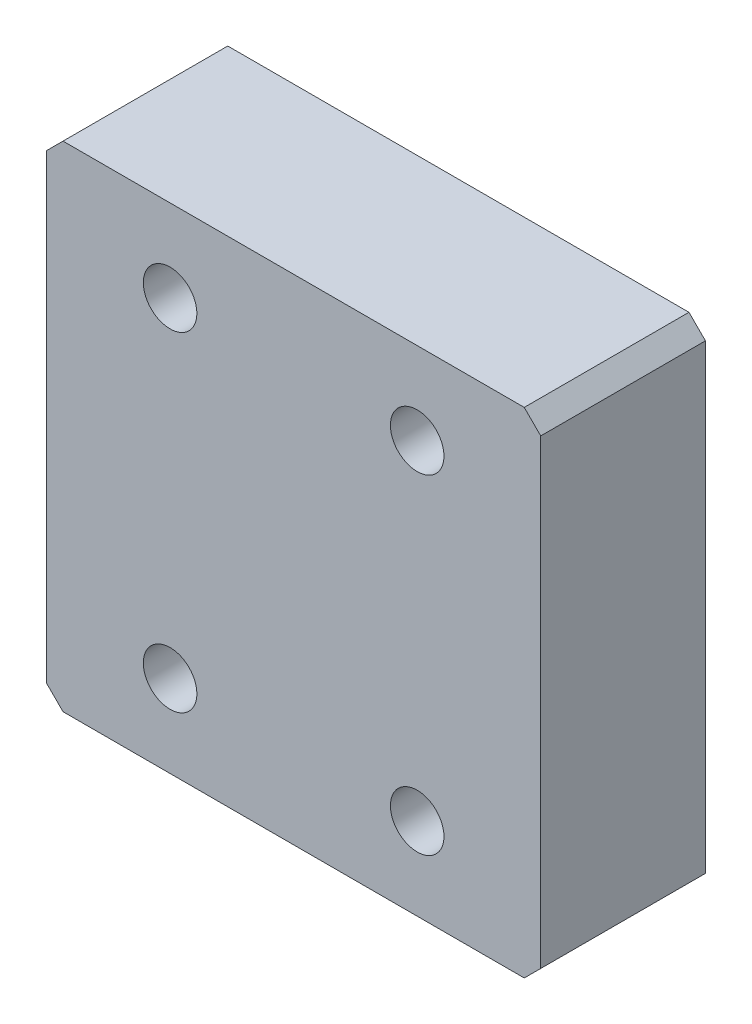
SolidWorks part; units mm, degrees
ref_plane "Front Plane" through (0, 0, 0) normal (0, 0, 1) x (1, 0, 0)
ref_plane "Top Plane" through (0, 0, 0) normal (0, 1, 0) x (1, 0, 0)
ref_plane "Right Plane" through (0, 0, 0) normal (1, 0, 0) x (0, 0, -1)
sketch "Sketch1" plane through (0, 0, 0) normal (0, 0, 1) x (1, 0, 0)
  line L1 (-30, 30) -> (30, 30)
  line L2 (-30, 30) -> (-30, -30)
  line L3 (-30, -30) -> (30, -30)
  line L4 (30, 30) -> (30, -30)
  line L5 (-30, 30) -> (30, -30) construction
  line L6 (-30, -30) -> (30, 30) construction
  circle A0 centre (-15, 20) radius 3.25
  circle A1 centre (15, 20) radius 3.25
  circle A2 centre (15, -20) radius 3.25
  circle A3 centre (-15, -20) radius 3.25
  point P0 (0, 0)
  point P10 (0, 0)
  point P13 (-16.567, 27.74)
  dimension "D3" = 6.5
  dimension "D1" = 60
  dimension "D2" = 60
  dimension "D4" = 15
  dimension "D5" = 10
extrude "Boss-Extrude1" add sketch "Sketch1" along normal blind 20
chamfer "Chamfer1" distance 2 angle 45 4 edges at (30, -30, 10) (-30, -30, 10) (-30, 30, 10) (30, 30, 10)
